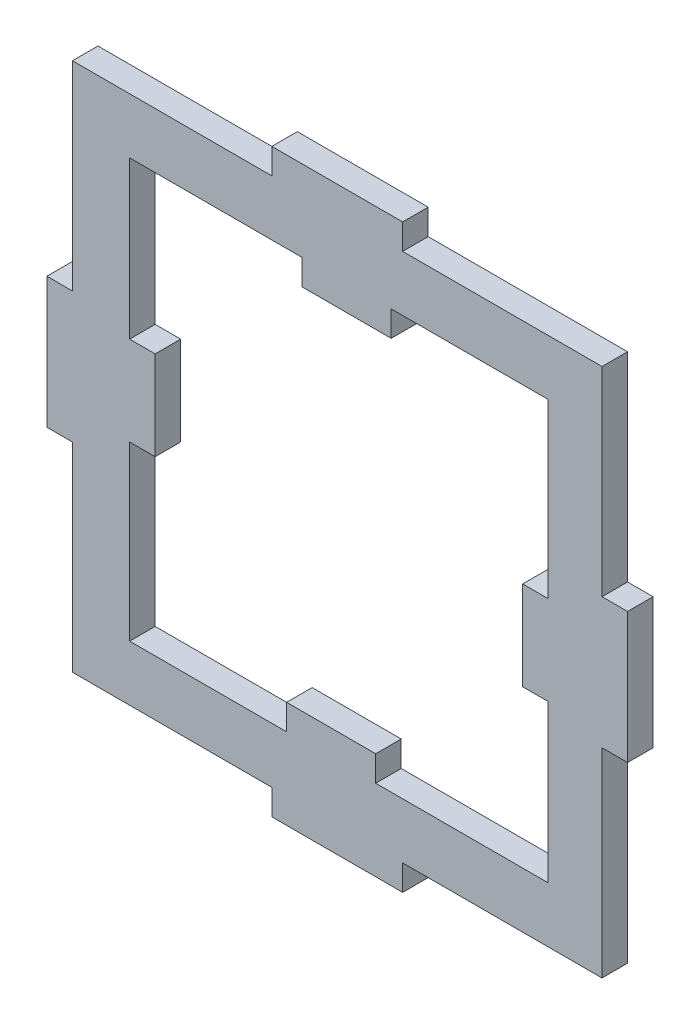
SolidWorks part; units mm, degrees
ref_plane "Front Plane" through (0, 0, 0) normal (0, 0, 1) x (1, 0, 0)
ref_plane "Top Plane" through (0, 0, 0) normal (0, 1, 0) x (1, 0, 0)
ref_plane "Right Plane" through (0, 0, 0) normal (1, 0, 0) x (0, 0, -1)
sketch "Sketch1" plane through (0, 0, 0) normal (0, 0, 1) x (1, 0, 0)
  line L0 (47.4, 11.7836) -> (52, 11.7836)
  line L1 (-48, -47.7) -> (-12.0836, -47.7)
  line L2 (-48, -47.7) -> (-48, -11.7836)
  line L3 (-48, 47.7) -> (-12.0836, 47.7)
  line L4 (47.4, -47.7) -> (47.4, -11.7836)
  line L7 (52, 11.7836) -> (52, -11.7836)
  line L8 (-12.0836, 47.7) -> (-12.0836, 52.3)
  line L9 (-12.0836, 52.3) -> (11.4836, 52.3)
  line L10 (11.4836, 47.7) -> (11.4836, 52.3)
  line L11 (47.4, 11.7836) -> (47.4, 47.7)
  line L12 (11.4836, -47.7) -> (47.4, -47.7)
  line L13 (47.4, -11.7836) -> (52, -11.7836)
  line L14 (11.4836, -47.7) -> (11.4836, -52.3)
  line L15 (11.4836, -52.3) -> (-12.0836, -52.3)
  line L16 (-12.0836, -47.7) -> (-12.0836, -52.3)
  line L17 (-48, -11.7836) -> (-52.6, -11.7836)
  line L18 (-52.6, -11.7836) -> (-52.6, 11.7836)
  line L19 (-48, 11.7836) -> (-52.6, 11.7836)
  line L20 (-48, 11.7836) -> (-48, 47.7)
  line L21 (11.4836, 47.7) -> (47.4, 47.7)
  point P0 (0, 0)
  point P6 (0, 48)
  point P8 (-120.029, -7.0586)
  point P12 (-25.2197, 46.4831)
  dimension "D1" = 95.4
  dimension "D2" = 95.4
  dimension "D3" = 4.6
  dimension "D4" = 4
extrude "Boss-Extrude1" add sketch "Sketch1" along normal blind 4.6
sketch "Sketch2" plane through (0, 0, 0) normal (0, 0, -1) x (-1, 0, 0)
  line L0 (9.4178, -37.7) -> (9.4178, -33.1)
  line L1 (-37.7, -37.7) -> (-6.6256, -37.7)
  line L2 (-37.7, -37.7) -> (-37.7, -9.4178)
  line L3 (-37.7, 37.7) -> (-9.4178, 37.7)
  line L4 (37.7, -37.7) -> (37.7, -6.6256)
  line L5 (-37.7, -37.7) -> (37.7, 37.7) construction
  line L6 (-37.7, 37.7) -> (37.7, -37.7) construction
  line L7 (37.7, 9.4178) -> (33.1, 9.4178)
  line L8 (9.4178, -33.1) -> (-6.6256, -33.1)
  line L9 (37.7, -6.6256) -> (33.1, -6.6256)
  line L10 (33.1, 9.4178) -> (33.1, -6.6256)
  line L11 (9.4178, -37.7) -> (37.7, -37.7)
  line L12 (-37.7, 6.6256) -> (-37.7, 37.7)
  line L13 (-6.6256, -37.7) -> (-6.6256, -33.1)
  line L14 (-37.7, -9.4178) -> (-33.1, -9.4178)
  line L15 (-33.1, -9.4178) -> (-33.1, 6.6256)
  line L16 (-37.7, 6.6256) -> (-33.1, 6.6256)
  line L17 (-9.4178, 37.7) -> (-9.4178, 33.1)
  line L18 (-9.4178, 33.1) -> (6.6256, 33.1)
  line L19 (6.6256, 37.7) -> (6.6256, 33.1)
  line L20 (6.6256, 37.7) -> (37.7, 37.7)
  line L21 (37.7, 9.4178) -> (37.7, 37.7)
  point P0 (0, 0)
  point P6 (38, 0)
  point P8 (-22.9432, 73.9665)
  dimension "D1" = 75.4
  dimension "D2" = 75.4
  dimension "D3" = 4.6
  dimension "D4" = 4
extrude "Cut-Extrude1" cut sketch "Sketch2" against normal through all
equation "\"mat\"=\"mat@levv1.assembly\""
equation "\"D1@Sketch1\"=100-\"mat\""
equation "\"D2@Sketch1\" = 100-\"mat\""
equation "\"D3@Sketch1\" = \"mat\""
equation "\"D1@Boss-Extrude1\"=\"mat\""
equation "\"D1@Sketch2\" = 80-\"mat\""
equation "\"D2@Sketch2\" = 80-\"mat\""
equation "\"D3@Sketch2\" = \"mat\""
